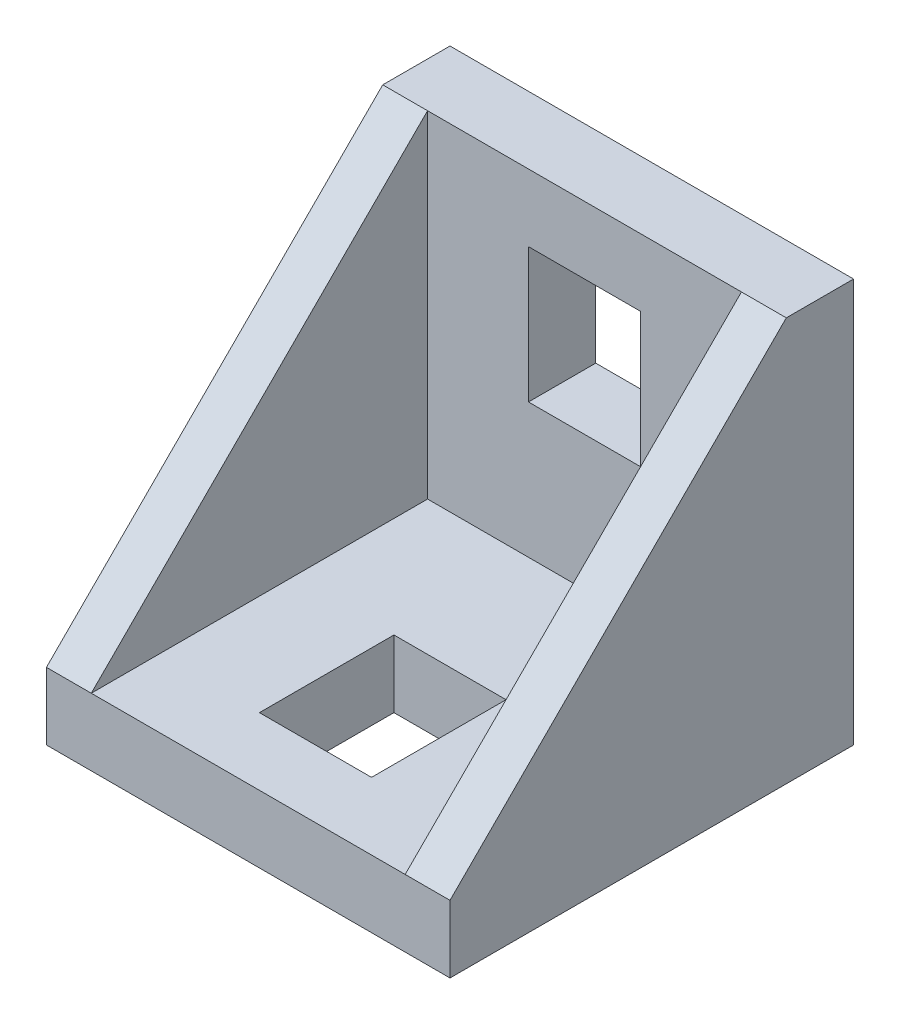
SolidWorks part; units mm, degrees
ref_plane "Front Plane" through (0, 0, 0) normal (0, 0, 1) x (1, 0, 0)
ref_plane "Top Plane" through (0, 0, 0) normal (0, 1, 0) x (1, 0, 0)
ref_plane "Right Plane" through (0, 0, 0) normal (1, 0, 0) x (0, 0, -1)
sketch "Sketch1" plane through (0, 0, 0) normal (0, 0, 1) x (1, 0, 0)
  line L1 (0, 0) -> (18, 0)
  line L2 (0, 0) -> (0, 18)
  line L3 (0, 18) -> (18, 18)
  line L4 (18, 0) -> (18, 18)
  dimension "D1" = 18
  dimension "D2" = 18
extrude "Extrude1" add sketch "Sketch1" along normal blind 3
sketch "Sketch2" plane through (0, 0, 3) normal (0, 0, 1) x (1, 0, 0)
  line L0 (18, 0) -> (18, 18) construction
  line L1 (0, 0) -> (18, 0)
  line L2 (0, 0) -> (0, 3)
  line L3 (0, 3) -> (18, 3)
  line L4 (18, 0) -> (18, 3)
  dimension "D1" = 3
extrude "Extrude2" add sketch "Sketch2" along normal blind 15
sketch "Sketch5" plane through (18, 0, 0) normal (1, 0, 0) x (0, 0, -1)
  line L0 (-3, 18) -> (-18, 3)
  line L1 (-18, 3) -> (-3, 3)
  line L2 (-3, 3) -> (-3, 18)
extrude "Extrude3" add sketch "Sketch5" against normal blind 2
sketch "Sketch6" plane through (0, 0, 0) normal (-1, 0, 0) x (0, 0, 1)
  line L0 (3, 18) -> (18, 3)
  line L1 (18, 3) -> (3, 3)
  line L2 (3, 3) -> (3, 18)
extrude "Extrude4" add sketch "Sketch6" against normal blind 2
sketch "Sketch7" plane through (0, 3, 0) normal (0, 1, 0) x (1, 0, 0)
  line L0 (9, -3) -> (9, -18) construction
  line L1 (16, -3) -> (2, -3) construction
  line L2 (16, -18) -> (2, -18) construction
  line L3 (6.5, -15) -> (6.5, -9)
  line L4 (11.5, -9) -> (11.5, -15)
  line L5 (6.5, -12) -> (11.5, -12) construction
  line L6 (11.5, -15) -> (6.5, -15)
  line L7 (11.5, -9) -> (6.5, -9)
  point P14 (9, -15)
  point P15 (9, -9)
  dimension "D1" = 5
  dimension "D2" = 3
  dimension "D3" = 6
extrude "Cut-Extrude1" cut sketch "Sketch7" against normal up to next
sketch "Sketch8" plane through (0, 0, 3) normal (0, 0, 1) x (-1, 0, 0)
  line L0 (-9, -3) -> (-9, -18) construction
  line L1 (-11.5, -15) -> (-6.5, -15)
  line L2 (-11.5, -9) -> (-6.5, -9)
  line L3 (-11.5, -15) -> (-11.5, -9)
  line L4 (-6.5, -9) -> (-6.5, -15)
  line L5 (-11.5, -12) -> (-6.5, -12) construction
  line L6 (-16, -18) -> (-2, -18) construction
  line L7 (-16, -3) -> (-2, -3) construction
  point P8 (-9, -15)
  point P10 (-9, -9)
  dimension "D1" = 5
  dimension "D2" = 3
  dimension "D3" = 6
extrude "Cut-Extrude2" cut sketch "Sketch8" against normal up to next
